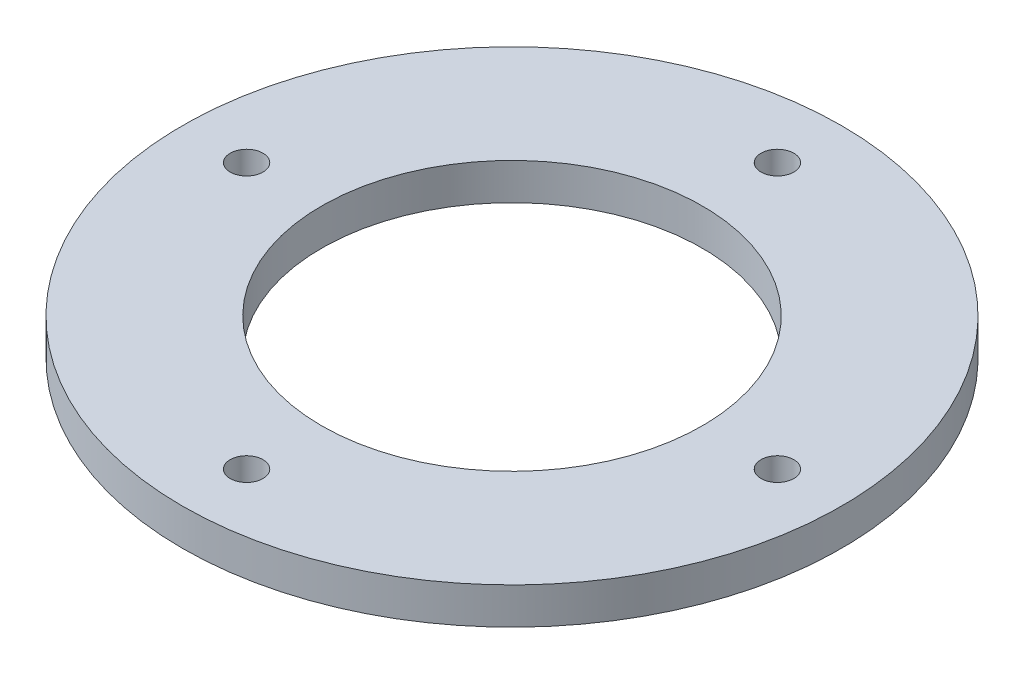
SolidWorks part; units mm, degrees
ref_plane "Front Plane" through (0, 0, 0) normal (0, 0, 1) x (1, 0, 0)
ref_plane "Top Plane" through (0, 0, 0) normal (0, 1, 0) x (1, 0, 0)
ref_plane "Right Plane" through (0, 0, 0) normal (1, 0, 0) x (0, 0, -1)
sketch "Sketch1" plane through (0, 0, 0) normal (0, 1, 0) x (1, 0, 0)
  circle A0 centre (0, 0) radius 16.51
  circle A1 centre (0, 0) radius 28.575
  circle A2 centre (23.0124, 0) radius 1.4224
  circle A3 centre (0, -23.0124) radius 1.4224
  circle A4 centre (-23.0124, 0) radius 1.4224
  circle A5 centre (0, 23.0124) radius 1.4224
  point P15 (0, 0)
  dimension "D1" = 33.02
  dimension "D2" = 57.15
  dimension "D4" = 2.8448
  dimension "D3" = 23.0124
  dimension "D5" = 4
extrude "Boss-Extrude1" add sketch "Sketch1" along normal blind 3.175
